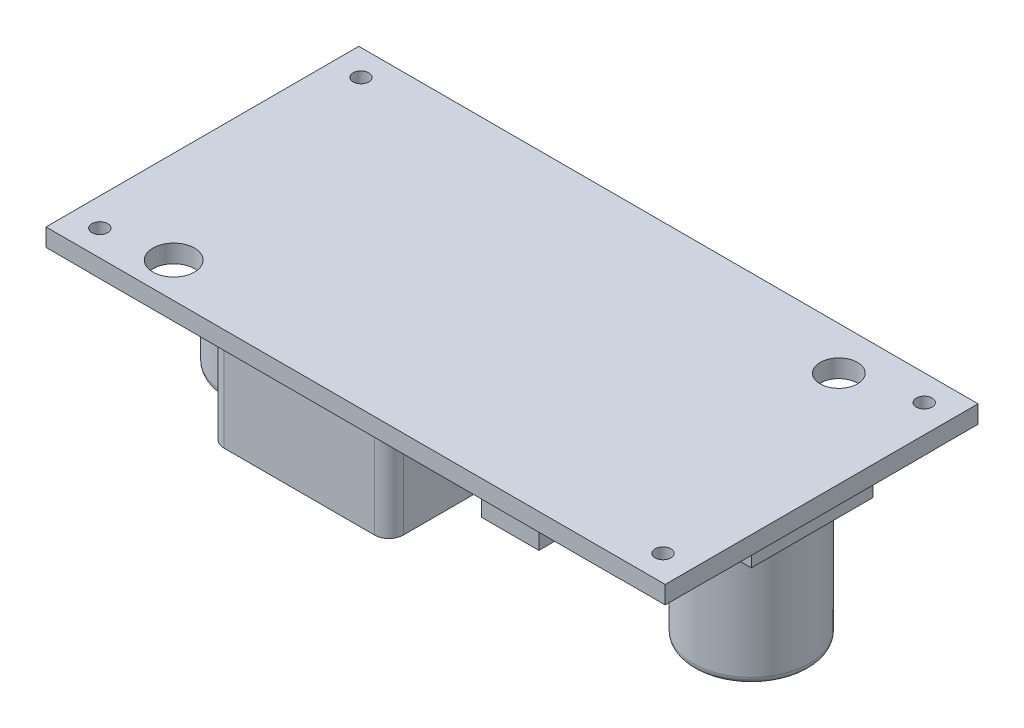
SolidWorks part; units mm, degrees
ref_plane "Front Plane" through (0, 0, 0) normal (0, 0, 1) x (1, 0, 0)
ref_plane "Top Plane" through (0, 0, 0) normal (0, 1, 0) x (1, 0, 0)
ref_plane "Right Plane" through (0, 0, 0) normal (1, 0, 0) x (0, 0, -1)
sketch "Sketch1" plane through (0, 0, 0) normal (0, 1, 0) x (1, 0, 0)
  line L1 (-21.575, -10.9) -> (21.575, -10.9)
  line L2 (-21.575, -10.9) -> (-21.575, 10.9)
  line L3 (-21.575, 10.9) -> (21.575, 10.9)
  line L4 (21.575, -10.9) -> (21.575, 10.9)
  line L5 (-21.575, -10.9) -> (21.575, 10.9) construction
  line L6 (-21.575, 10.9) -> (21.575, -10.9) construction
  point P0 (0, 0)
  dimension "D1" = 21.8
  dimension "D2" = 43.15
extrude "Boss-Extrude1" add sketch "Sketch1" along normal blind 1.25
sketch "Sketch2" plane through (0, 1.25, 0) normal (0, 1, 0) x (1, 0, 0)
  line L4 (21.575, 10.9) -> (-21.575, 10.9) construction
  line L5 (21.575, -10.9) -> (21.575, 10.9) construction
  line L6 (-21.575, -10.9) -> (21.575, -10.9) construction
  line L7 (-21.575, 10.9) -> (-21.575, -10.9) construction
  circle A0 centre (19.625, 9.1) radius 0.55
  circle A1 centre (19.625, -9.1) radius 0.55
  circle A2 centre (-19.625, 9.1) radius 0.55
  circle A3 centre (-19.625, -9.1) radius 0.55
  point P16 (20.175, 9.1)
  point P17 (19.625, 9.65)
  point P18 (-20.175, 9.1)
  point P19 (-19.625, -9.65)
  dimension "D3" = 1.1
  dimension "D1" = 1.4
  dimension "D2" = 1.25
  dimension "D4" = 1.4
  dimension "D5" = 1.25
extrude "Cut-Extrude1" cut sketch "Sketch2" against normal through all
sketch "Sketch3" plane through (0, 1.25, 0) normal (0, 1, 0) x (1, 0, 0)
  line L1 (-21.575, 10.9) -> (-21.575, -10.9) construction
  line L3 (21.575, 10.9) -> (-21.575, 10.9) construction
  line L4 (-21.575, -10.9) -> (21.575, -10.9) construction
  circle A0 centre (14.875, 7.9) radius 1.3
  circle A1 centre (-15.125, -8.45) radius 1.45
  point P4 (-16.575, -8.45)
  point P7 (16.175, 7.9)
  point P10 (14.875, 9.2)
  point P11 (-15.125, -9.9)
  dimension "D1" = 2.6
  dimension "D2" = 2.9
  dimension "D3" = 30
  dimension "D4" = 5
  dimension "D5" = 1.7
  dimension "D6" = 1
extrude "Cut-Extrude2" cut sketch "Sketch3" against normal through all
sketch "Sketch4" plane through (0, 0, 0) normal (0, -1, 0) x (1, 0, 0)
  line L1 (21.575, -10.9) -> (18.575, -10.9)
  line L2 (21.575, -10.9) -> (21.575, -7.9)
  line L3 (21.575, -7.9) -> (18.575, -7.9)
  line L4 (18.575, -10.9) -> (18.575, -7.9)
  line L5 (21.575, 10.9) -> (18.575, 10.9)
  line L6 (21.575, 10.9) -> (21.575, 7.9)
  line L7 (21.575, 7.9) -> (18.575, 7.9)
  line L8 (18.575, 10.9) -> (18.575, 7.9)
  line L9 (-21.575, 10.9) -> (-18.575, 10.9)
  line L10 (-21.575, 10.9) -> (-21.575, 7.9)
  line L11 (-21.575, 7.9) -> (-18.575, 7.9)
  line L12 (-18.575, 10.9) -> (-18.575, 7.9)
  line L13 (-21.575, -10.9) -> (-18.575, -10.9)
  line L14 (-21.575, -10.9) -> (-21.575, -7.9)
  line L15 (-21.575, -7.9) -> (-18.575, -7.9)
  line L16 (-18.575, -10.9) -> (-18.575, -7.9)
  dimension "D1" = 3
extrude "Cut-Extrude3" cut sketch "Sketch4" against normal blind 0.01
sketch "Sketch5" plane through (0, 0, 0) normal (0, -1, 0) x (1, 0, 0)
  line L0 (20.7466, -6.7043) -> (18.394, -6.7043) construction
  line L1 (20.7466, 7.55) -> (18.394, 7.55) construction
  line L2 (-17.7724, -6.7043) -> (-20.4941, -6.7043) construction
  line L3 (-17.7724, 7.55) -> (-20.4941, 7.55) construction
  text T0 "IN+" font "Century Gothic" height 1
  text T1 "IN-" font "Century Gothic" height 1
  text T2 "OUT+" font "Century Gothic" height 1
  text T3 "OUT-" font "Century Gothic" height 1
extrude "Cut-Extrude4" cut sketch "Sketch5" against normal blind 0.01
sketch "Sketch6" plane through (0, 0, 0) normal (0, -1, 0) x (1, 0, 0)
  line L0 (-18.575, 10.9) -> (18.575, 10.9) construction
  line L1 (12.075, 3.9) -> (20.575, 3.9)
  line L2 (12.075, 3.9) -> (12.075, -4.6)
  line L3 (12.075, -4.6) -> (20.575, -4.6)
  line L4 (20.575, 3.9) -> (20.575, -4.6)
  line L5 (12.075, 3.9) -> (20.575, -4.6) construction
  line L6 (12.075, -4.6) -> (20.575, 3.9) construction
  line L7 (-20.575, 3.9) -> (-12.075, 3.9)
  line L8 (-20.575, 3.9) -> (-20.575, -4.6)
  line L9 (-20.575, -4.6) -> (-12.075, -4.6)
  line L10 (-12.075, 3.9) -> (-12.075, -4.6)
  line L11 (-20.575, 3.9) -> (-12.075, -4.6) construction
  line L12 (-20.575, -4.6) -> (-12.075, 3.9) construction
  line L13 (-21.575, -7.9) -> (-21.575, 7.9) construction
  line L14 (21.575, 7.9) -> (21.575, -7.9) construction
  point P0 (16.325, -0.35)
  point P5 (-16.325, -0.35)
  dimension "D1" = 8.5
  dimension "D2" = 7
  dimension "D3" = 1
  dimension "D4" = 1
extrude "Boss-Extrude2" add sketch "Sketch6" along normal blind 1.75
sketch "Sketch7" plane through (0, -1.75, 0) normal (0, -1, 0) x (1, 0, 0)
  line L0 (20.575, 3.9) -> (12.075, 3.9) construction
  line L1 (-12.075, -4.6) -> (-12.075, 3.9) construction
  line L2 (-12.075, 3.9) -> (-20.575, 3.9) construction
  line L3 (12.075, 3.9) -> (12.075, -4.6) construction
  circle A0 centre (-16.325, -0.35) radius 4.05
  circle A1 centre (16.325, -0.35) radius 4.05
  point P6 (16.325, 3.9)
  point P9 (-12.075, -0.35)
  point P12 (-16.325, 3.9)
  point P15 (12.075, -0.35)
  dimension "D1" = 8.1
extrude "Boss-Extrude3" add sketch "Sketch7" along normal blind 8.5
fillet "Fillet1" radius 0.5 2 edges at (16.325, -10.25, -4.4) (-16.325, -10.25, -4.4)
sketch "Sketch8" plane through (0, 0, 0) normal (0, -1, 0) x (1, 0, 0)
  line L0 (-18.575, 10.9) -> (18.575, 10.9) construction
  line L1 (-11.375, 9.7) -> (1.125, 9.7)
  line L2 (-11.375, 9.7) -> (-11.375, -2.8)
  line L3 (-11.375, -2.8) -> (1.125, -2.8)
  line L4 (1.125, 9.7) -> (1.125, -2.8)
  line L5 (-21.575, -7.9) -> (-21.575, 7.9) construction
  dimension "D1" = 12.5
  dimension "D2" = 1.2
  dimension "D3" = 10.2
extrude "Boss-Extrude4" add sketch "Sketch8" along normal blind 7.1
fillet "Fillet2" radius 1 4 edges at (-11.375, -3.55, -2.8) (1.125, -3.55, -2.8) (1.125, -3.55, 9.7) (-11.375, -3.55, 9.7)
sketch "Sketch9" plane through (0, 0, 0) normal (0, -1, 0) x (1, 0, 0)
  line L0 (-10.225, -4.5) -> (-10.225, -5.2)
  line L1 (-10.925, -4.5) -> (-10.225, -4.5)
  line L2 (-10.925, -4.5) -> (-10.925, -9.5)
  line L3 (-10.925, -9.5) -> (-1.425, -9.5)
  line L4 (-1.425, -4.5) -> (-1.425, -9.5)
  line L5 (-10.225, -5.2) -> (-2.125, -5.2)
  line L6 (-2.125, -5.2) -> (-2.125, -4.5)
  line L7 (-2.125, -4.5) -> (-1.425, -4.5)
  line L8 (-6.175, -5.2) -> (-6.175, -9.5) construction
  line L9 (18.575, -10.9) -> (-18.575, -10.9) construction
  line L10 (-21.575, -7.9) -> (-21.575, 7.9) construction
  dimension "D1" = 9.5
  dimension "D2" = 5
  dimension "D3" = 4.3
  dimension "D4" = 1.4
  dimension "D5" = 10.65
extrude "Boss-Extrude5" add sketch "Sketch9" along normal blind 10
sketch "Sketch10" plane through (0, 0, 0) normal (0, -1, 0) x (1, 0, 0)
  line L0 (21.575, 7.9) -> (21.575, -7.9) construction
  line L1 (7.575, 9.7) -> (11.575, 9.7)
  line L2 (7.575, 9.7) -> (7.575, 7.2)
  line L3 (7.575, 7.2) -> (11.575, 7.2)
  line L4 (11.575, 9.7) -> (11.575, 7.2)
  line L5 (-18.575, 10.9) -> (18.575, 10.9) construction
  dimension "D1" = 4
  dimension "D2" = 2.5
  dimension "D3" = 10
  dimension "D4" = 1.2
extrude "Boss-Extrude6" add sketch "Sketch10" along normal blind 2.3
sketch "Sketch11" plane through (0, 0, 0) normal (0, -1, 0) x (1, 0, 0)
  line L0 (1.125, -1.8) -> (1.125, 8.7) construction
  line L1 (1.625, 0.6) -> (11.625, 0.6)
  line L2 (1.625, 0.6) -> (1.625, -7.8)
  line L3 (1.625, -7.8) -> (11.625, -7.8)
  line L4 (11.625, 0.6) -> (11.625, -7.8)
  line L5 (18.575, -10.9) -> (-18.575, -10.9) construction
  dimension "D1" = 8.4
  dimension "D2" = 10
  dimension "D3" = 0.5
  dimension "D4" = 3.1
extrude "Boss-Extrude7" add sketch "Sketch11" along normal blind 4.3
chamfer "Chamfer1" distance 2 angle 20 2 edges at (6.625, -4.3, 0.6) (6.625, -4.3, -7.8)
sketch "Sketch12" plane through (0, 0, 0) normal (0, -1, 0) x (1, 0, 0)
  line L0 (11.625, -7.8) -> (11.625, 0.6) construction
  line L1 (1.625, -7.8) -> (11.625, -7.8)
  line L2 (1.625, -7.8) -> (1.625, -9.3)
  line L3 (1.625, -9.3) -> (11.625, -9.3)
  line L4 (11.625, -7.8) -> (11.625, -9.3)
  dimension "D1" = 1.5
extrude "Boss-Extrude8" add sketch "Sketch12" along normal blind 1
sketch "Sketch13" plane through (0, 0, 0) normal (0, -1, 0) x (1, 0, 0)
  line L0 (11.625, 0.6) -> (1.625, 0.6) construction
  line L1 (2.375, 5.6) -> (3.375, 5.6)
  line L2 (2.375, 5.6) -> (2.375, 0.6)
  line L3 (2.375, 0.6) -> (3.375, 0.6)
  line L4 (3.375, 5.6) -> (3.375, 0.6)
  line L5 (1.625, -0.1279) -> (1.625, 0.6) construction
  dimension "D1" = 0.75
  dimension "D2" = 1
  dimension "D3" = 5
extrude "Boss-Extrude9" add sketch "Sketch13" along normal blind 1
pattern_linear "LPattern1" count 5 spacing 1.9 along (1, 0, 0) of "Boss-Extrude9"
sketch "Sketch14" plane through (0, -10, 0) normal (0, -1, 0) x (1, 0, 0)
  line L0 (-10.925, -9.5) -> (-1.425, -9.5) construction
  line L1 (-1.425, -9.5) -> (-1.425, -4.5) construction
  circle A0 centre (-2.575, -8.2) radius 1.15
  dimension "D1" = 2.3
  dimension "D2" = 1.3
extrude "Boss-Extrude10" add sketch "Sketch14" along normal blind 1.6
